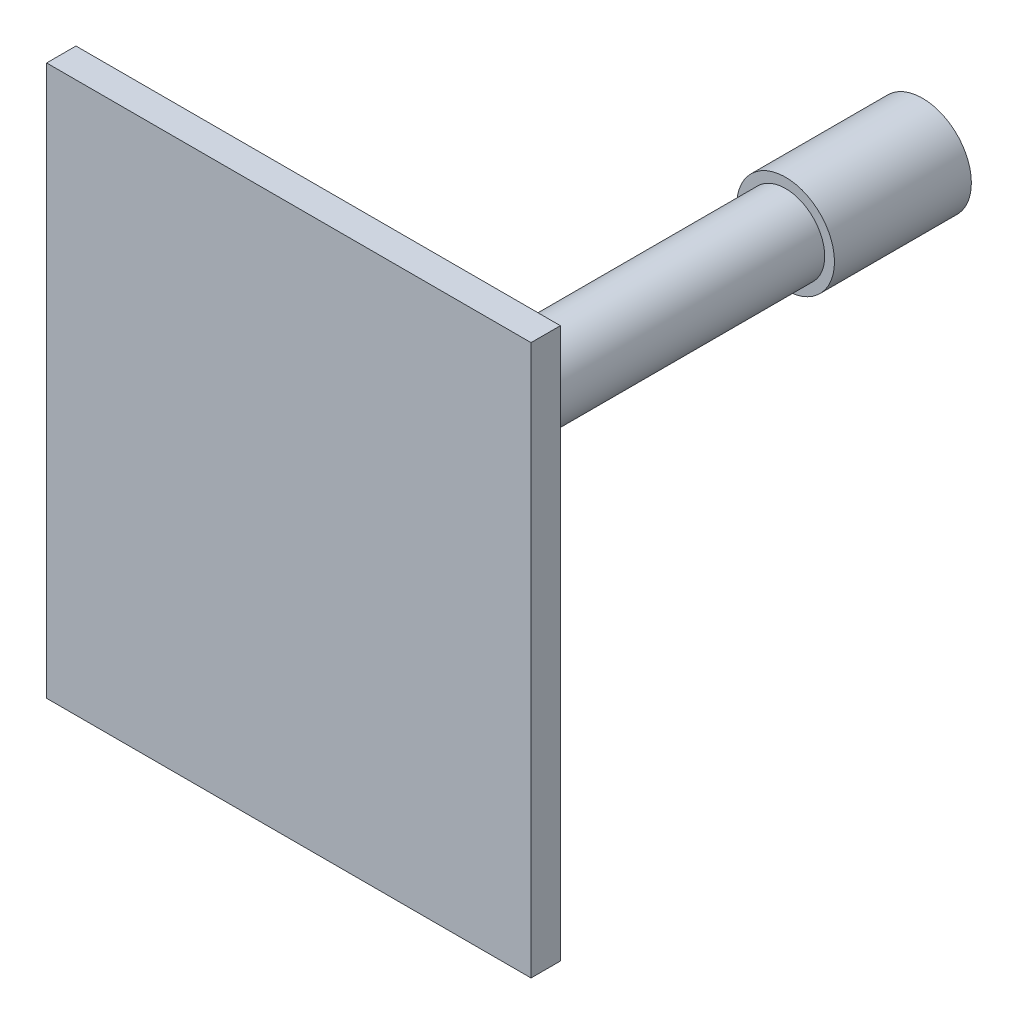
SolidWorks part; units mm, degrees
ref_plane "Front Plane" through (0, 0, 0) normal (0, 0, 1) x (1, 0, 0)
ref_plane "Top Plane" through (0, 0, 0) normal (0, 1, 0) x (1, 0, 0)
ref_plane "Right Plane" through (0, 0, 0) normal (1, 0, 0) x (0, 0, -1)
sketch "Sketch2" plane through (0, 0, 0) normal (0, 0, 1) x (1, 0, 0)
  circle A0 centre (0, 0) radius 15.875
extrude "Boss-Extrude1" add sketch "Sketch2" along normal blind 44.45
sketch "Sketch3" plane through (0, 0, 44.45) normal (0, 0, 1) x (1, 0, 0)
  circle A0 centre (0, 0) radius 12.7
extrude "Boss-Extrude2" add sketch "Sketch3" along normal blind 113.665
sketch "Sketch4" plane through (0, 0, 158.115) normal (0, 0, 1) x (1, 0, 0)
  circle A0 centre (0, 0) radius 11.0173
extrude "Boss-Extrude3" add sketch "Sketch4" along normal blind 38.1
sketch "Sketch5" plane through (0, 0, 196.215) normal (0, 0, 1) x (1, 0, 0)
  circle A0 centre (0, 0) radius 9.525
extrude "Boss-Extrude4" [suppressed] add sketch "Sketch5" along normal blind 203.2
sketch "Sketch6" plane through (0, 0, 0) normal (0, 0, -1) x (-1, 0, 0)
  circle A0 centre (0, 0) radius 5.5562
extrude "Cut-Extrude1" cut sketch "Sketch6" against normal blind 215.9
sketch "Sketch7" [suppressed] plane through (0, 0, 399.415) normal (0, 0, 1) x (1, 0, 0)
  line L0 (-9.525, 0) -> (9.525, 0) construction
  line L1 (-9.525, 0) -> (9.525, 0)
  line L2 (9.525, 0) -> (9.525, 11.8308)
  line L3 (9.525, 11.8308) -> (-9.525, 11.8308)
  line L4 (-9.525, 11.8308) -> (-9.525, 0)
  circle A0 centre (0, 0) radius 9.525 construction
extrude "Cut-Extrude2" [suppressed] cut sketch "Sketch7" against normal up to surface (203.2 mm away)
sketch "Sketch8" plane through (0, 0, 196.215) normal (0, 0, 1) x (1, 0, 0)
  line L1 (-78.6428, 89.3315) -> (78.6428, 89.3315)
  line L2 (-78.6428, 89.3315) -> (-78.6428, -89.3315)
  line L3 (-78.6428, -89.3315) -> (78.6428, -89.3315)
  line L4 (78.6428, 89.3315) -> (78.6428, -89.3315)
  line L5 (-78.6428, 89.3315) -> (78.6428, -89.3315) construction
  line L6 (-78.6428, -89.3315) -> (78.6428, 89.3315) construction
  point P0 (0, 0)
extrude "Boss-Extrude5" add sketch "Sketch8" along normal blind 9.525
